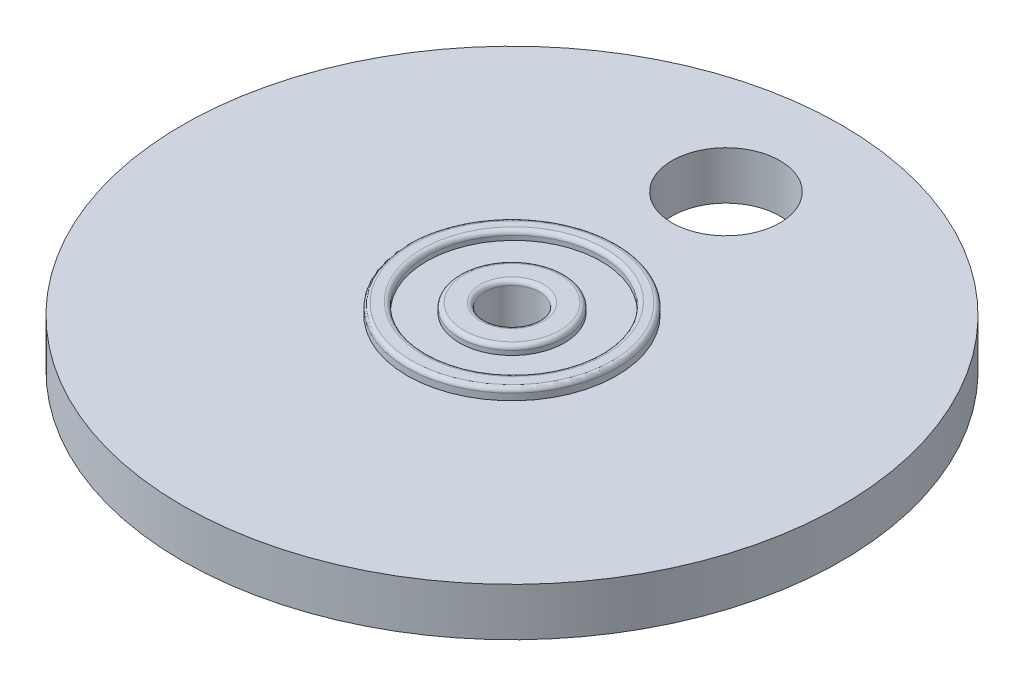
SolidWorks part; units mm, degrees
ref_plane "Alzado" through (0, 0, 0) normal (0, 0, 1) x (1, 0, 0)
ref_plane "Planta" through (0, 0, 0) normal (0, 1, 0) x (1, 0, 0)
ref_plane "Vista lateral" through (0, 0, 0) normal (1, 0, 0) x (0, 0, -1)
sketch "Croquis1" plane through (0, 0, 0) normal (0, 1, 0) x (1, 0, 0)
  circle A0 centre (0, 0) radius 12
  circle A1 centre (0, 0) radius 3.125
  dimension "D1" = 24
  dimension "D2" = 6.25
extrude "Saliente-Extruir1" add sketch "Croquis1" along normal blind 8
sketch "Croquis3" plane through (0, 8, 0) normal (0, 1, 0) x (1, 0, 0)
  circle A0 centre (0, 0) radius 6
  circle A1 centre (0, 0.2176) radius 10
  dimension "D1" = 12
  dimension "D2" = 20
extrude "Cortar-Extruir1" cut sketch "Croquis3" against normal blind 1
sketch "Croquis4" plane through (0, 0, 0) normal (0, -1, 0) x (1, 0, 0)
  circle A0 centre (0, 0) radius 6 construction
  circle A1 centre (0, 0) radius 6
  circle A2 centre (0, -0.2176) radius 10 construction
  circle A3 centre (0, -0.2176) radius 10
extrude "Cortar-Extruir2" cut sketch "Croquis4" against normal blind 1
fillet "Redondeo1" radius 0.5 8 edges at (0, 0, 12) (0, 0, -10.2176) (0, 0, -6) (0, 0, 3.125) (0, 8, 3.125) (0, 8, 6) (0, 8, 12) (0, 8, 9.7824)
ref_plane "Plano1" through (0, 4, 0) normal (0, 1, 0) x (1, 0, 0)
sketch "Croquis5" plane through (0, 4, 0) normal (0, 1, 0) x (1, 0, 0)
  circle A0 centre (0, 0) radius 12 construction
  circle A1 centre (0, 0) radius 12
  circle A2 centre (0, 0) radius 37.75
  dimension "D1" = 75.5
extrude "Saliente-Extruir2" add sketch "Croquis5" along normal mid plane 5.5
sketch "Croquis6" plane through (0, 6.75, 0) normal (0, 1, 0) x (1, 0, 0)
  circle A0 centre (0, 24.5083) radius 6.1825
extrude "Cortar-Extruir3" cut sketch "Croquis6" against normal through all
